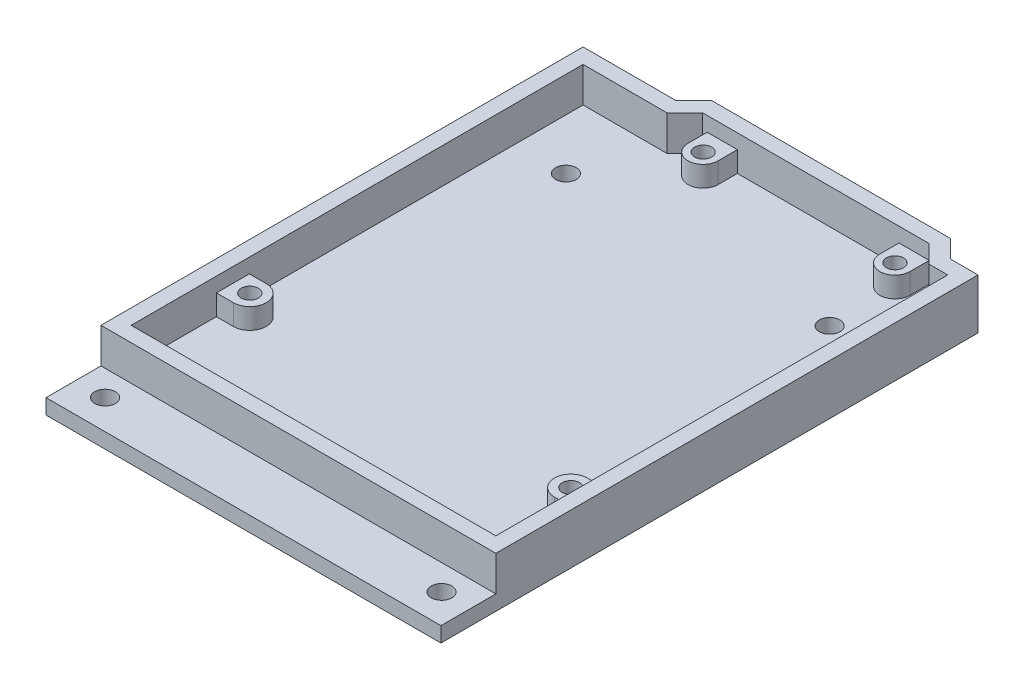
SolidWorks part; units mm, degrees
ref_plane "Front Plane" through (0, 0, 0) normal (0, 0, 1) x (1, 0, 0)
ref_plane "Top Plane" through (0, 0, 0) normal (0, 1, 0) x (1, 0, 0)
ref_plane "Right Plane" through (0, 0, 0) normal (1, 0, 0) x (0, 0, -1)
sketch "Sketch1" plane through (0, 0, 0) normal (0, 1, 0) x (1, 0, 0)
  line L0 (-15.25, 39.1) -> (-12.65, 41.7)
  line L1 (-28.75, -39.1) -> (28.75, -39.1)
  line L2 (-28.75, -39.1) -> (-28.75, 39.1)
  line L3 (-28.75, 39.1) -> (-15.25, 39.1)
  line L4 (28.75, -39.1) -> (28.75, 39.1)
  line L5 (-28.75, -39.1) -> (28.75, 39.1) construction
  line L6 (-28.75, 39.1) -> (28.75, -39.1) construction
  line L7 (-12.65, 41.7) -> (22.15, 41.7)
  line L8 (22.15, 41.7) -> (24.75, 39.1)
  line L9 (24.75, 39.1) -> (28.75, 39.1)
  point P0 (0, 0)
  point P9 (-9.9287, 41.7)
  point P11 (21.8653, 39.1)
  point P12 (-15.6353, 39.1)
  point P13 (22.4088, 39.1)
  point P14 (-14.6842, 39.1)
  point P15 (26.2928, 39.1)
  dimension "D1" = 57.5
  dimension "D2" = 78.2
  dimension "D3" = 80.8
  dimension "D4" = 34.8
  dimension "D5" = 4
extrude "Boss-Extrude1" add sketch "Sketch1" along normal blind 2.2
sketch "Sketch3" plane through (0, 2.2, 0) normal (0, 1, 0) x (1, 0, 0)
  line L0 (-28.75, 39.1) -> (-15.25, 39.1)
  line L1 (-15.25, 39.1) -> (-12.65, 41.7)
  line L2 (-12.65, 41.7) -> (22.15, 41.7)
  line L3 (22.15, 41.7) -> (24.75, 39.1)
  line L4 (24.75, 39.1) -> (28.75, 39.1)
  line L5 (28.75, 39.1) -> (28.75, -31.1)
  line L6 (28.75, -39.1) -> (28.75, 39.1) construction
  line L7 (28.75, -31.1) -> (-28.75, -31.1)
  line L8 (-28.75, 39.1) -> (-28.75, -39.1) construction
  line L9 (-28.75, -31.1) -> (-28.75, 39.1)
  dimension "D1" = 72.8
extrude "Extrude-Thin1" add sketch "Sketch3" along normal blind 5.12 thin
sketch "Sketch4" plane through (0, 2.2, 0) normal (0, 1, 0) x (1, 0, 0)
  line L0 (21.2387, 39.5) -> (-11.7387, 39.5) construction
  line L1 (-11.08, 39.5) -> (-6.68, 39.5)
  line L2 (-11.08, 39.5) -> (-11.08, 36.7)
  line L4 (-6.68, 39.5) -> (-6.68, 36.7)
  line L5 (16.85, 39.5) -> (21.25, 39.5)
  line L6 (16.85, 39.5) -> (16.85, 36.7)
  line L7 (21.25, 39.5) -> (21.25, 36.7)
  line L8 (-11.08, 36.7) -> (-6.68, 36.7) construction
  line L9 (16.85, 36.7) -> (21.25, 36.7) construction
  line L10 (-8.88, 36.7) -> (19.05, 36.7) construction
  line L11 (22.15, 41.7) -> (-12.65, 41.7) construction
  line L12 (28.75, -31.1) -> (28.75, 39.1) construction
  line L13 (26.55, -28.9) -> (26.55, 36.9) construction
  line L14 (26.55, -12.83) -> (23.8, -12.83)
  line L15 (26.55, -12.83) -> (26.55, -17.63)
  line L16 (26.55, -17.63) -> (23.8, -17.63)
  line L18 (-26.55, 36.9) -> (-26.55, -28.9) construction
  line L19 (-26.55, -11.69) -> (-24.0864, -11.69)
  line L20 (-26.55, -11.69) -> (-26.55, -16.49)
  line L21 (-26.55, -16.49) -> (-24.0864, -16.49)
  arc A0 (-11.08, 36.7) -> (-6.68, 36.7) centre (-8.88, 36.7) ccw
  arc A1 (16.85, 36.7) -> (21.25, 36.7) centre (19.05, 36.7) ccw
  arc A2 (-24.0864, -16.49) -> (-24.0864, -11.69) centre (-24.0864, -14.09) ccw
  arc A3 (23.8, -12.83) -> (23.8, -17.63) centre (23.8, -15.23) ccw
  point P29 (26.55, -12.1)
  dimension "D1" = 27.93
  dimension "D2" = 5
  dimension "D3" = 9.7
  dimension "D4" = 4.4
  dimension "D5" = 4.8
  dimension "D6" = 47.9
  dimension "D7" = 4.95
  dimension "D8" = 51.93
  dimension "D9" = 50.79
extrude "Boss-Extrude2" add sketch "Sketch4" along normal blind 3
sketch "Sketch6" plane through (0, 7.32, 0) normal (0, 1, 0) x (1, 0, 0)
  line L0 (-19.15, 27) -> (19.25, 27) construction
  line L1 (28.75, -31.1) -> (28.75, 39.1) construction
  line L2 (-24.45, -34.8) -> (24.55, -34.8) construction
  line L3 (28.75, -39.1) -> (28.75, -31.1) construction
  circle A0 centre (-8.88, 36.7) radius 1.25
  circle A1 centre (19.05, 36.7) radius 1.25
  circle A2 centre (23.8, -15.23) radius 1.25
  circle A3 centre (-24.0864, -14.09) radius 1.25
  circle A4 centre (-19.15, 27) radius 1.5
  circle A5 centre (19.25, 27) radius 1.5
  circle A6 centre (-24.45, -34.8) radius 1.5
  circle A7 centre (24.55, -34.8) radius 1.5
  dimension "D1" = 2.5
  dimension "D2" = 9.7
  dimension "D3" = 9.5
  dimension "D5" = 3
  dimension "D6" = 4.2
  dimension "D9" = 3
  dimension "D4" = 38.4
  dimension "D7" = 49
  dimension "D8" = 71.5
extrude "Cut-Extrude1" cut sketch "Sketch6" against normal through all
